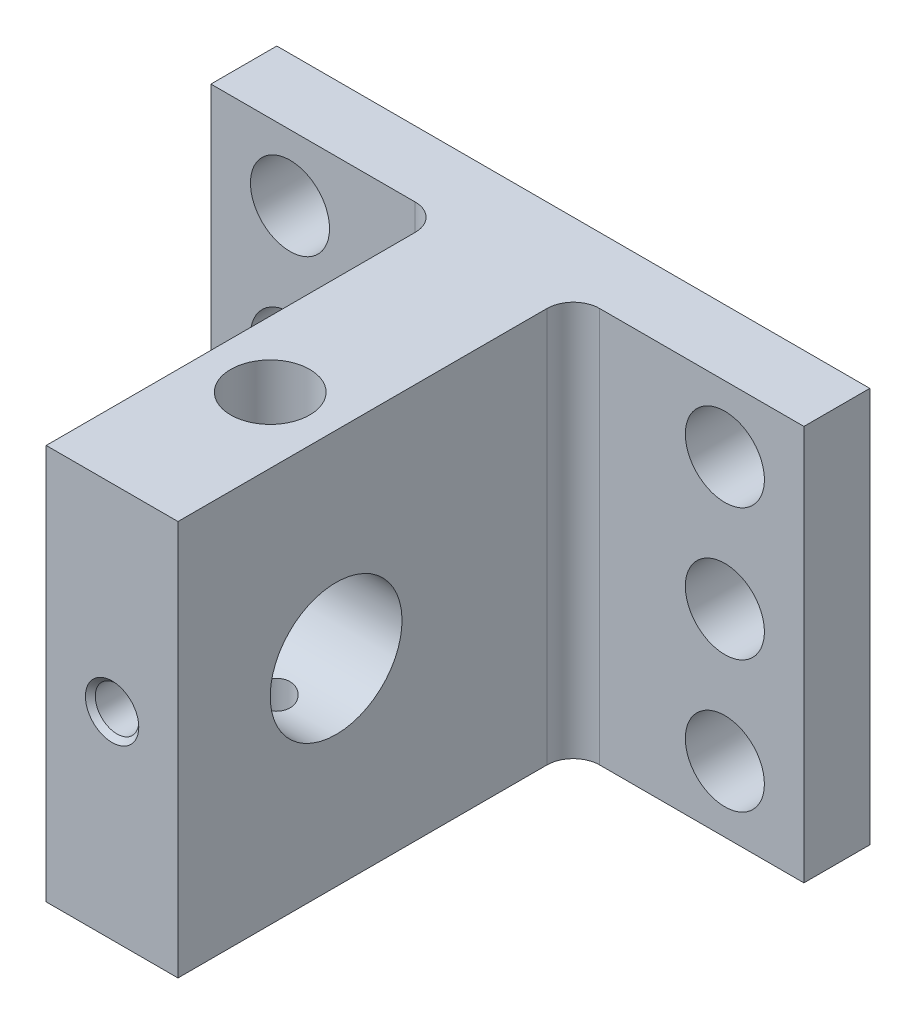
SolidWorks part; units mm, degrees
ref_plane "Piano frontale" through (0, 0, 0) normal (0, 0, 1) x (1, 0, 0)
ref_plane "Piano superiore" through (0, 0, 0) normal (0, 1, 0) x (1, 0, 0)
ref_plane "Piano destro" through (0, 0, 0) normal (1, 0, 0) x (0, 0, -1)
sketch "Sketch1" plane through (0, 0, 0) normal (0, 0, 1) x (1, 0, 0)
  line L0 (-22.5, 15) -> (22.5, -15) construction
  line L1 (-22.5, 15) -> (22.5, 15)
  line L2 (-22.5, 15) -> (-22.5, -15)
  line L3 (-22.5, -15) -> (22.5, -15)
  line L4 (22.5, 15) -> (22.5, -15)
  line L5 (-22.5, -15) -> (22.5, 15) construction
  point P4 (0, 0)
  dimension "D1" = 30
  dimension "D2" = 45
extrude "Base" add sketch "Sketch1" along normal blind 5
sketch "Sketch2" plane through (0, 0, 5) normal (0, 0, 1) x (1, 0, 0)
  line L0 (-5, 15) -> (5, -15) construction
  line L1 (-5, 15) -> (5, 15)
  line L2 (-5, 15) -> (-5, -15)
  line L3 (-5, -15) -> (5, -15)
  line L4 (5, 15) -> (5, -15)
  line L5 (-5, -15) -> (5, 15) construction
  line L6 (22.5, 0) -> (-22.5, 0) construction
  line L7 (22.5, -15) -> (22.5, 15) construction
  line L8 (-22.5, 15) -> (-22.5, -15) construction
  point P10 (0, 0)
  dimension "D1" = 30
  dimension "D2" = 10
extrude "Boss-Extrude2" add sketch "Sketch2" along normal blind 30
sketch "Sketch3" plane through (-5, 0, 0) normal (-1, 0, 0) x (0, 0, 1)
  line L0 (35, 15) -> (35, -15) construction
  line L1 (35, 15) -> (5, 15) construction
  circle A0 centre (23, 0) radius 5
  dimension "D1" = 10
  dimension "D2" = 12
  dimension "D3" = 15
extrude "Cut-Extrude3" cut sketch "Sketch3" against normal blind 10
sketch "Sketch9" plane through (0, 0, 5) normal (0, 0, 1) x (1, 0, 0)
  line L0 (-16.5, 15) -> (-16.5, -15) construction
  line L2 (-22.5, 0) -> (22.5, 0) construction
  line L3 (-22.5, 15) -> (-22.5, -15) construction
  line L4 (22.5, -15) -> (22.5, 15) construction
  line L5 (0, 15) -> (0, -15) construction
  line L6 (22.5, 15) -> (5, 15) construction
  line L7 (-22.5, -15) -> (-5, -15) construction
  circle A1 centre (-16.5, 10) radius 3
  circle A7 centre (-16.5, 0) radius 3
  circle A8 centre (-16.5, -10) radius 3
  circle A9 centre (16.5, -10) radius 3
  circle A10 centre (16.5, 0) radius 3
  circle A11 centre (16.5, 10) radius 3
  point P2 (0, 0)
  dimension "D1" = 5
  dimension "D2" = 6
  dimension "D3" = 6
extrude "Screw" cut sketch "Sketch9" against normal blind 5
sketch "Sketch10" plane through (0, 15, 0) normal (0, 1, 0) x (1, 0, 0)
  line L0 (5, -35) -> (-5, -35) construction
  circle A0 centre (0, -23) radius 3
  dimension "D2" = 6
  dimension "D1" = 12
extrude "Top hole" cut sketch "Sketch10" against normal blind 15
sketch "Sketch11" plane through (0, -15, 0) normal (0, -1, 0) x (1, 0, 0)
  line L0 (-5, 35) -> (5, 35) construction
  circle A0 centre (0, 23) radius 1.5
  dimension "D1" = 3
  dimension "D2" = 12
extrude "Bottom hole" cut sketch "Sketch11" against normal blind 15
sketch "Sketch17" plane through (0, 0, 35) normal (0, 0, 1) x (1, 0, 0)
  line L0 (0, 15) -> (0, -15) construction
  line L1 (5, 15) -> (-5, 15) construction
  line L2 (-5, -15) -> (5, -15) construction
  line L3 (-5, 0) -> (5, 0) construction
  line L4 (-5, 15) -> (-5, -15) construction
  line L5 (5, -15) -> (5, 15) construction
  point P12 (0, 0)
fillet "Fillet1" radius 2 1 edges at (-5, 0, 5)
fillet "Fillet2" radius 2 1 edges at (5, 0, 5)
hole_wizard "M4 Tapped Hole3" positions "3DSketch9" profile "Sketch21" tap size "M4" standard "ISO"
sketch3d "3DSketch9"
  point P0 (0, 0, 35)
sketch "Sketch21" plane through (0, 0, 35) normal (1, 0, 0) x (0, -1, 0)
  line L0 (0, 0) -> (0, 11.0914)
  line L1 (0, 11.0914) -> (1.65, 10.1)
  line L2 (1.65, 10.1) -> (1.65, 0.375)
  line L3 (1.65, 0.375) -> (2.025, 0)
  line L5 (2.025, 0) -> (0, 0)
  line L6 (-1.65, 0.375) -> (-2.025, 0) construction
  line L10 (0, 11.0914) -> (-1.65, 10.1) construction
  line L11 (0, -6.35) -> (0, 107.95) construction
  dimension "Tap Drill Dia." = 3.3
  dimension "Tap Drill Depth" = 10.1
  dimension "Near C'Sink Dia." = 4.05
  dimension "Near C'Sink Angle" = 90
  dimension "Drill Angle" = 118
cosmetic thread "Hole Thread2" parameters "D1"=7.2801, "D2"=4
